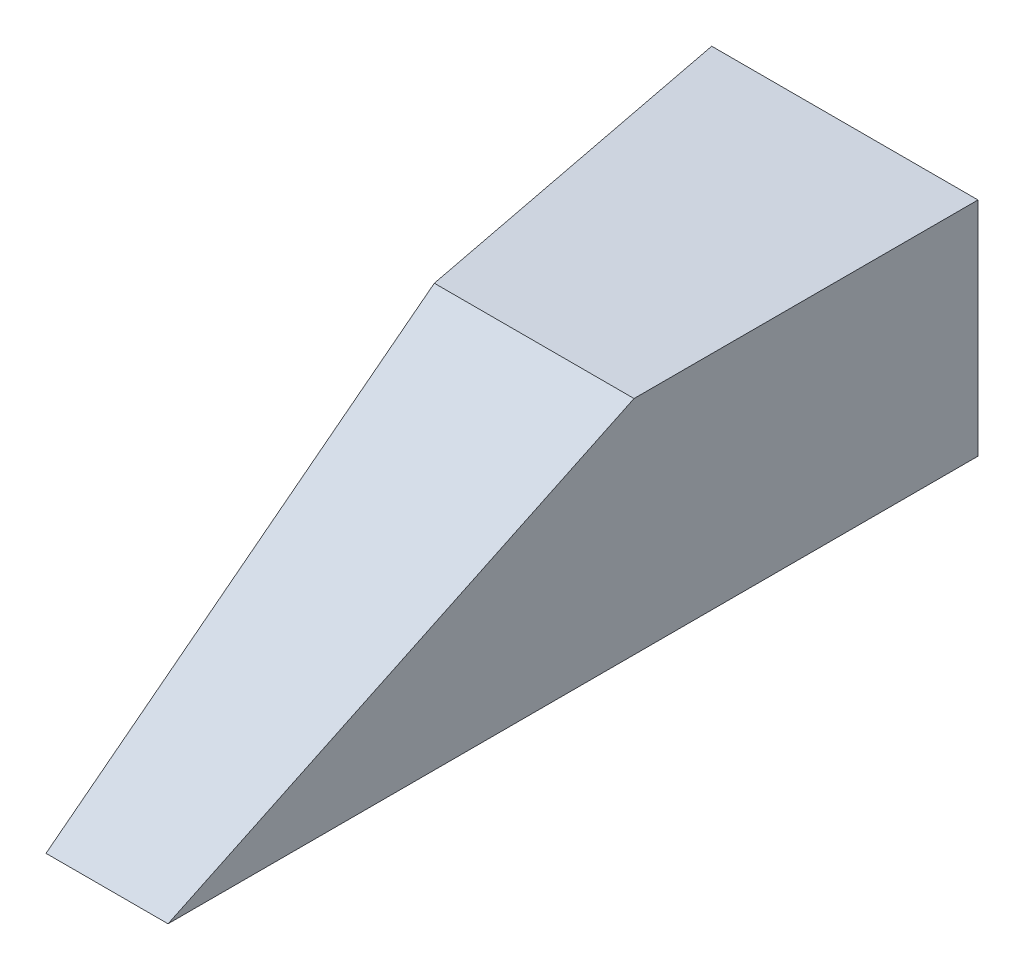
SolidWorks part; units mm, degrees
ref_plane "Front Plane" through (0, 0, 0) normal (0, 0, 1) x (1, 0, 0)
ref_plane "Top Plane" through (0, 0, 0) normal (0, 1, 0) x (1, 0, 0)
ref_plane "Right Plane" through (0, 0, 0) normal (1, 0, 0) x (0, 0, -1)
sketch "Sketch1" plane through (0, 0, 0) normal (0, 1, 0) x (1, 0, 0)
  line L0 (0, 1066.8) -> (0, 0)
  line L1 (0, 0) -> (279.4, 0)
  line L2 (279.4, 0) -> (457.2, 1066.8)
  line L3 (457.2, 1066.8) -> (0, 1066.8)
  dimension "D1" = 279.4
  dimension "D2" = 457.2
  dimension "D3" = 1066.8
extrude "Boss-Extrude1" add sketch "Sketch1" along normal blind 508
sketch "Sketch2" plane through (0, 0, 0) normal (-1, 0, 0) x (0, 0, 1)
  line L0 (0, 0) -> (-1066.8, 508)
  line L1 (-1066.8, 508) -> (-1066.8, 732.6724)
  line L2 (-1066.8, 732.6724) -> (0, 732.6724)
  line L3 (0, 732.6724) -> (0, 0)
extrude "Cut-Extrude1" cut sketch "Sketch2" against normal blind 508
sketch "Sketch3" plane through (0, 0, 0) normal (0, -1, 0) x (1, 0, 0)
  line L0 (0, -1066.8) -> (0, -1854.2)
  line L1 (0, -1854.2) -> (609.6, -1854.2)
  line L2 (609.6, -1854.2) -> (457.2, -1066.8)
  line L3 (457.2, -1066.8) -> (0, -1066.8)
  dimension "D1" = 787.4
  dimension "D2" = 609.6
extrude "Boss-Extrude2" add sketch "Sketch3" against normal blind 508
mirror "Mirror1" about plane through (0, 508, -1066.8) normal (1, 0, 0) of "Boss-Extrude1", "Cut-Extrude1", "Boss-Extrude2"
sketch "Sketch4" plane through (0, 0, 0) normal (0, 1, 0) x (1, 0, 0)
  line L1 (0, 0) -> (1308.8939, 0)
  line L2 (0, 0) -> (0, 2214.8087)
  line L3 (0, 2214.8087) -> (1308.8939, 2214.8087)
  line L4 (1308.8939, 0) -> (1308.8939, 2214.8087)
extrude "Cut-Extrude2" cut sketch "Sketch4" along normal through all
